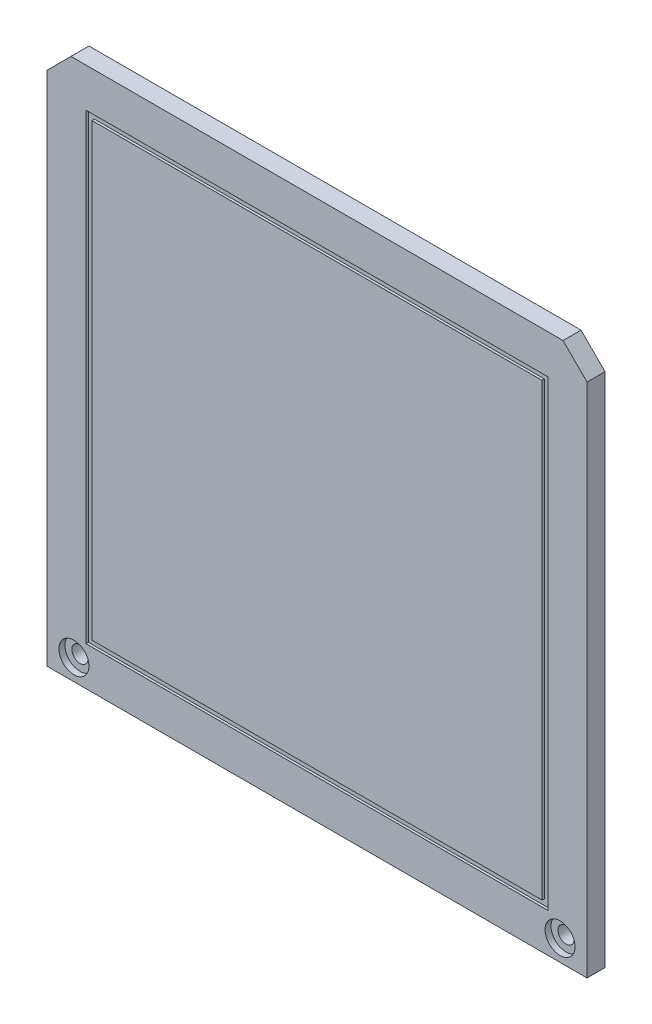
SolidWorks part; units mm, degrees
ref_plane "Front Plane" through (0, 0, 0) normal (0, 0, 1) x (1, 0, 0)
ref_plane "Top Plane" through (0, 0, 0) normal (0, 1, 0) x (1, 0, 0)
ref_plane "Right Plane" through (0, 0, 0) normal (1, 0, 0) x (0, 0, -1)
sketch "Sketch1" plane through (0, 0, 0) normal (0, 0, 1) x (1, 0, 0)
  line L1 (-45, -45) -> (45, -45)
  line L2 (-45, -45) -> (-45, 45)
  line L3 (-45, 45) -> (45, 45)
  line L4 (45, -45) -> (45, 45)
  line L5 (-45, -45) -> (45, 45) construction
  line L6 (-45, 45) -> (45, -45) construction
  point P0 (0, 0)
  dimension "D1" = 90
  dimension "D2" = 90
extrude "Boss-Extrude1" add sketch "Sketch1" along normal blind 3
sketch "Sketch2" plane through (0, 0, 3) normal (0, 0, 1) x (1, 0, 0)
  line L0 (-40.5, -41.5) -> (40.5, -41.5) construction
  line L1 (-45, -45) -> (45, -45) construction
  line L2 (-45, 45) -> (-45, -45) construction
  circle A0 centre (-40.5, -41.5) radius 1.35
  circle A1 centre (40.5, -41.5) radius 1.35
  point P3 (0, -41.5)
  dimension "D1" = 2.7
  dimension "D3" = 4.5
  dimension "D2" = 3.5
extrude "Cut-Extrude1" cut sketch "Sketch2" against normal through all
sketch "Sketch3" plane through (0, 0, 3) normal (0, 0, 1) x (1, 0, 0)
  line L1 (-38.5, -38.5) -> (38.5, -38.5)
  line L2 (-38.5, -38.5) -> (-38.5, 38.5)
  line L3 (-38.5, 38.5) -> (38.5, 38.5)
  line L4 (38.5, -38.5) -> (38.5, 38.5)
  line L5 (-38.5, -38.5) -> (38.5, 38.5) construction
  line L6 (-38.5, 38.5) -> (38.5, -38.5) construction
  line L7 (-37.5, -37.5) -> (37.5, -37.5)
  line L8 (-37.5, -37.5) -> (-37.5, 37.5)
  line L9 (-37.5, 37.5) -> (37.5, 37.5)
  line L10 (37.5, -37.5) -> (37.5, 37.5)
  line L11 (-37.5, -37.5) -> (37.5, 37.5) construction
  line L12 (-37.5, 37.5) -> (37.5, -37.5) construction
  point P0 (0, 0)
  point P6 (0, 0)
  point P11 (-41.6657, 41.6657)
  dimension "D1" = 75
  dimension "D2" = 1
extrude "Cut-Extrude2" cut sketch "Sketch3" against normal blind 0.4
sketch "Sketch4" plane through (0, 0, 0) normal (0, 0, -1) x (-1, 0, 0)
  line L4 (-38.5, 38.5) -> (-38.5, -38.5)
  line L5 (38.5, 38.5) -> (-38.5, 38.5)
  line L6 (38.5, -38.5) -> (38.5, 38.5)
  line L7 (-38.5, -38.5) -> (38.5, -38.5)
  line L8 (-38.5, 38.5) -> (-38.5, -38.5)
  line L9 (38.5, 38.5) -> (-38.5, 38.5)
  line L10 (38.5, -38.5) -> (38.5, 38.5)
  line L11 (-38.5, -38.5) -> (38.5, -38.5)
  line L12 (-37.5, 37.5) -> (-37.5, -37.5)
  line L13 (37.5, 37.5) -> (-37.5, 37.5)
  line L14 (37.5, -37.5) -> (37.5, 37.5)
  line L15 (-37.5, -37.5) -> (37.5, -37.5)
  line L16 (-37.5, 37.5) -> (-37.5, -37.5)
  line L17 (37.5, 37.5) -> (-37.5, 37.5)
  line L18 (37.5, -37.5) -> (37.5, 37.5)
  line L19 (-37.5, -37.5) -> (37.5, -37.5)
  dimension "D1" = 0
  dimension "D2" = 0
extrude "Cut-Extrude3" cut sketch "Sketch4" against normal blind 0.4
chamfer "Chamfer1" distance 4 angle 45 2 edges at (45, 45, 1.5) (-45, 45, 1.5)
sketch "Sketch5" plane through (0, 0, 3) normal (0, 0, 1) x (1, 0, 0)
  circle A0 centre (-40.5, -41.5) radius 2.5
  circle A1 centre (40.5, -41.5) radius 2.5
  dimension "D1" = 5
extrude "Cut-Extrude4" cut sketch "Sketch5" against normal blind 1
